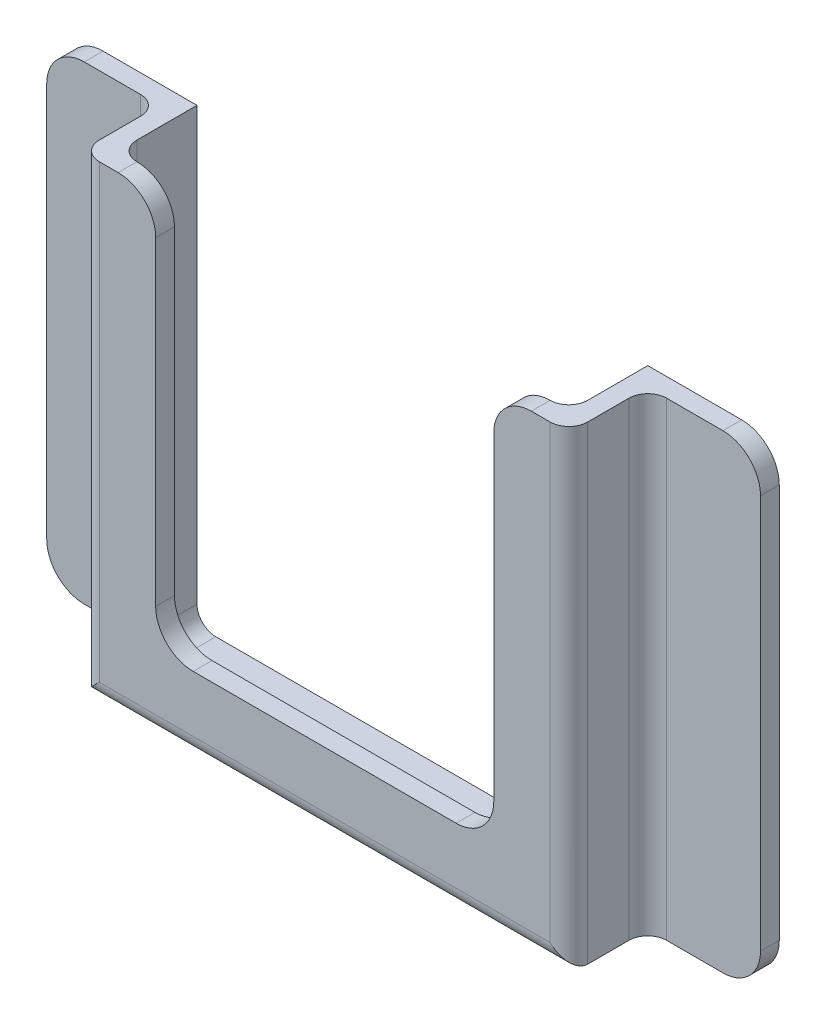
SolidWorks part; units mm, degrees
ref_plane "Front Plane" through (0, 0, 0) normal (0, 0, 1) x (1, 0, 0)
ref_plane "Top Plane" through (0, 0, 0) normal (0, 1, 0) x (1, 0, 0)
ref_plane "Right Plane" through (0, 0, 0) normal (1, 0, 0) x (0, 0, -1)
sketch "Sketch1" plane through (0, 0, 0) normal (0, 0, 1) x (1, 0, 0)
  line L0 (60, 60) -> (62.5, 60)
  line L1 (0, 0) -> (60, 0)
  line L2 (0, 0) -> (0, 60)
  line L4 (60, 0) -> (60, 60)
  line L5 (-2.5, -2.5) -> (62.5, -2.5)
  line L6 (-2.5, -2.5) -> (-2.5, 60)
  line L7 (-2.5, 60) -> (0, 60)
  line L8 (62.5, -2.5) -> (62.5, 60)
  dimension "D1" = 60
  dimension "D2" = 60
  dimension "D3" = 2.5
  dimension "D4" = 2.5
  dimension "D5" = 2.5
extrude "Boss-Extrude1" add sketch "Sketch1" along normal blind 10.5
sketch "Sketch2" plane through (0, 0, 10.5) normal (0, 0, 1) x (1, 0, 0)
  line L0 (52.5, 60) -> (62.5, 60)
  line L1 (-2.5, -2.5) -> (62.5, -2.5)
  line L2 (-2.5, -2.5) -> (-2.5, 60)
  line L3 (-2.5, 60) -> (7.5, 60)
  line L4 (62.5, -2.5) -> (62.5, 60)
  line L6 (7.5, 60) -> (7.5, 7.5)
  line L7 (7.5, 7.5) -> (52.5, 7.5)
  line L8 (52.5, 60) -> (52.5, 7.5)
  dimension "D1" = 10
  dimension "D2" = 10
  dimension "D3" = 10
extrude "Boss-Extrude2" add sketch "Sketch2" along normal blind 2.5
sketch "Sketch3" plane through (0, 0, 0) normal (0, 0, -1) x (-1, 0, 0)
  line L0 (2.5, -2.5) -> (-62.5, -2.5) construction
  line L1 (-62.5, -2.5) -> (-77.5, -2.5)
  line L2 (-62.5, -2.5) -> (-62.5, 60)
  line L3 (-62.5, 60) -> (-77.5, 60)
  line L4 (-77.5, -2.5) -> (-77.5, 60)
  line L5 (2.5, -2.5) -> (17.5, -2.5)
  line L6 (2.5, -2.5) -> (2.5, 60)
  line L7 (2.5, 60) -> (17.5, 60)
  line L8 (17.5, -2.5) -> (17.5, 60)
  line L9 (-7.5, 60) -> (0, 60) construction
  line L10 (2.5, 60) -> (2.5, -2.5) construction
  dimension "D1" = 15
  dimension "D2" = 15
extrude "Boss-Extrude3" add sketch "Sketch3" against normal blind 2.5
fillet "Fillet1" radius 2.5 9 edges at (0, 0, 5.25) (60, 0, 5.25) (62.5, 28.75, 13) (30, -2.5, 13) (-2.5, 28.75, 13) (60, 30, 10.5) (0, 30, 10.5) (-2.5, 28.75, 2.5) (62.5, 28.75, 2.5)
fillet "Fillet2" radius 5 8 edges at (7.5, 7.5, 11.75) (52.5, 7.5, 11.75) (-17.5, 60, 1.25) (-17.5, -2.5, 1.25) (77.5, -2.5, 1.25) (77.5, 60, 1.25) (52.5, 60, 11.75) (7.5, 60, 11.75)
